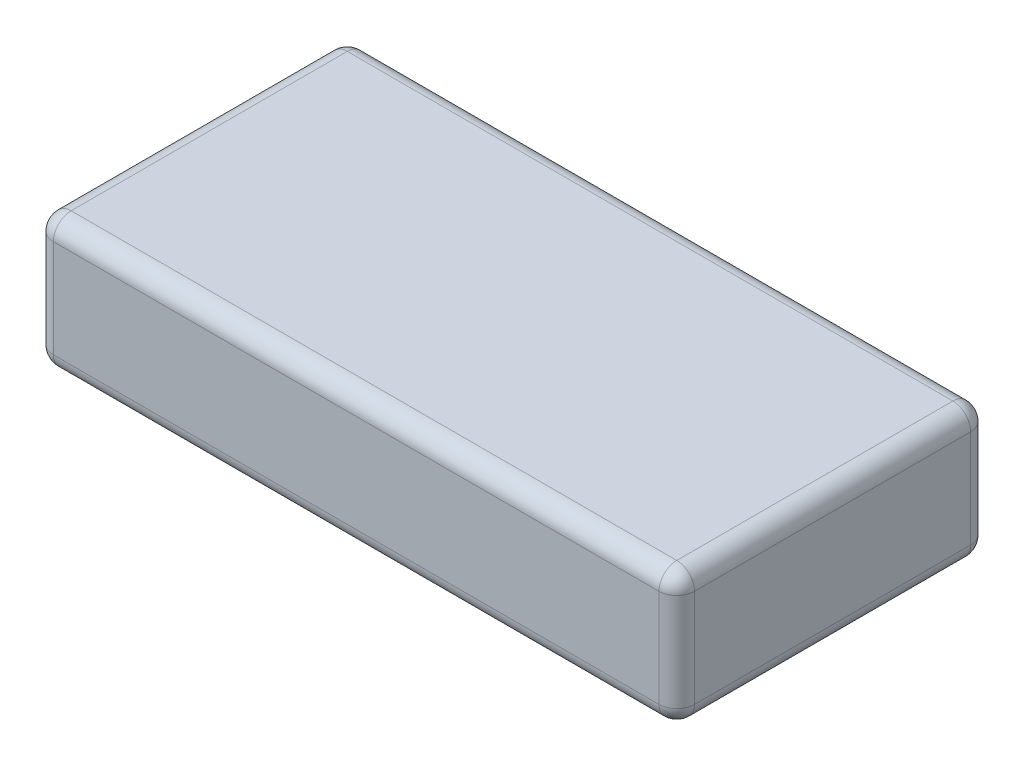
SolidWorks part; units mm, degrees
ref_plane "Front Plane" through (0, 0, 0) normal (0, 0, 1) x (1, 0, 0)
ref_plane "Top Plane" through (0, 0, 0) normal (0, 1, 0) x (1, 0, 0)
ref_plane "Right Plane" through (0, 0, 0) normal (1, 0, 0) x (0, 0, -1)
sketch "Sketch1" plane through (0, 0, 0) normal (0, 1, 0) x (1, 0, 0)
  line L1 (36, 17.5) -> (-36, 17.5)
  line L2 (36, 17.5) -> (36, -17.5)
  line L3 (36, -17.5) -> (-36, -17.5)
  line L4 (-36, 17.5) -> (-36, -17.5)
  line L5 (36, 17.5) -> (-36, -17.5) construction
  line L6 (36, -17.5) -> (-36, 17.5) construction
  point P0 (0, 0)
  dimension "D1" = 35
  dimension "D2" = 72
extrude "Boss-Extrude1" add sketch "Sketch1" along normal blind 15
fillet "Fillet1" radius 2 12 edges at (-36, 0, 0) (-36, 7.5, -17.5) (0, 0, -17.5) (36, 7.5, -17.5) (36, 0, 0) (-36, 7.5, 17.5) (36, 7.5, 17.5) (0, 0, 17.5) (0, 15, -17.5) (36, 15, 0) (0, 15, 17.5) (-36, 15, 0)
